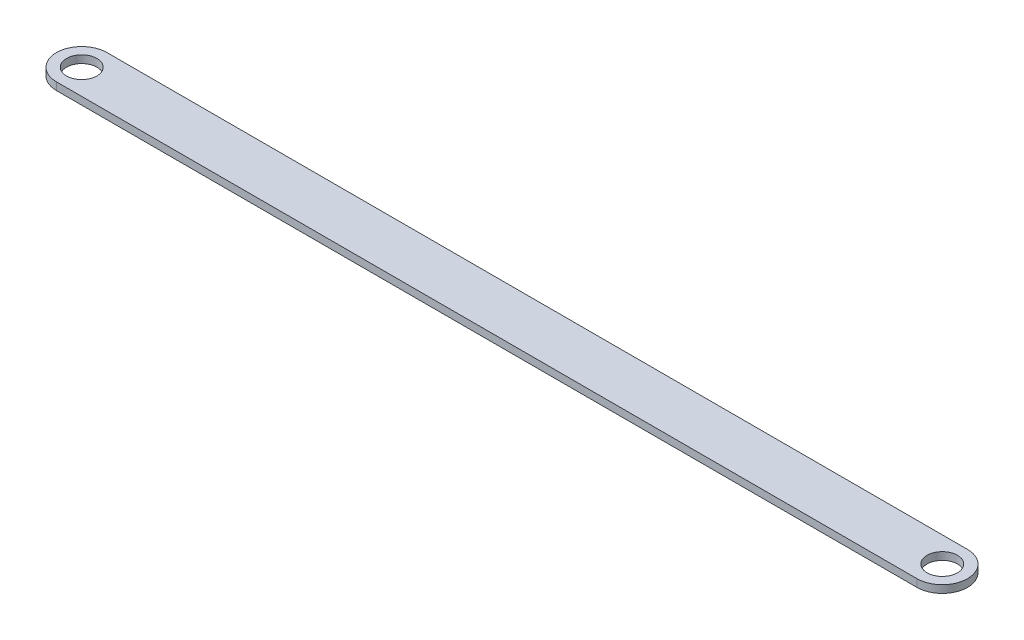
SolidWorks part; units mm, degrees
ref_plane "Front" through (0, 0, 0) normal (0, 0, 1) x (1, 0, 0)
ref_plane "Top" through (0, 0, 0) normal (0, 1, 0) x (1, 0, 0)
ref_plane "Right" through (0, 0, 0) normal (1, 0, 0) x (0, 0, -1)
sketch "Sketch1" plane through (0, 0, 0) normal (0, 1, 0) x (1, 0, 0)
  line L0 (-62.6876, 5.8571) -> (277.3124, 5.8571) construction
  line L1 (-62.6876, 15.8571) -> (277.3124, 15.8571)
  line L2 (-62.6876, -4.1429) -> (277.3124, -4.1429)
  arc A0 (-62.6876, 15.8571) -> (-62.6876, -4.1429) centre (-62.6876, 5.8571) ccw
  arc A1 (277.3124, -4.1429) -> (277.3124, 15.8571) centre (277.3124, 5.8571) ccw
  circle A2 centre (-62.6876, 5.8571) radius 6
  circle A3 centre (277.3124, 5.8571) radius 6
  point P2 (107.3124, 5.8571)
  dimension "D1" = 20
  dimension "D2" = 340
extrude "Boss-Extrude1" add sketch "Sketch1" along normal blind 3
